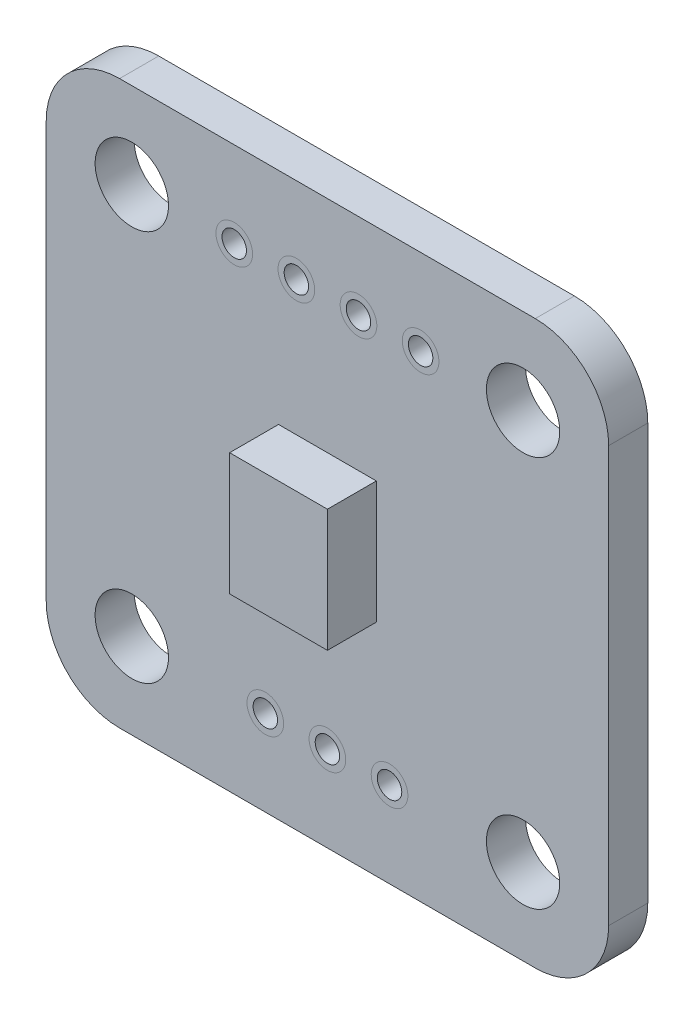
SolidWorks part; units mm, degrees
material "E-Glass Fiber"
ref_plane "Front Plane" through (0, 0, 0) normal (0, 0, 1) x (1, 0, 0)
ref_plane "Top Plane" through (0, 0, 0) normal (0, 1, 0) x (1, 0, 0)
ref_plane "Right Plane" through (0, 0, 0) normal (1, 0, 0) x (0, 0, -1)
sketch "Sketch1" plane through (0, 0, 0) normal (0, 0, 1) x (1, 0, 0)
  line L0 (0, 0) -> (0, -8) construction
  line L1 (-8.5, -11.5) -> (8.5, -11.5)
  line L2 (-11.5, -8.5) -> (-11.5, 8.5)
  line L3 (-8.5, 11.5) -> (8.5, 11.5)
  line L4 (11.5, -8.5) -> (11.5, 8.5)
  line L5 (-11.5, -11.5) -> (11.5, 11.5) construction
  line L6 (-11.5, 11.5) -> (11.5, -11.5) construction
  line L7 (-8, -8) -> (8, -8) construction
  line L8 (-8, -8) -> (-8, 8) construction
  line L9 (-8, 8) -> (8, 8) construction
  line L10 (8, -8) -> (8, 8) construction
  line L11 (-8, -8) -> (8, 8) construction
  line L12 (-8, 8) -> (8, -8) construction
  line L13 (2.54, -8) -> (-2.54, -8) construction
  line L14 (-1.27, 8) -> (1.27, 8) construction
  line L15 (-3.81, 8) -> (3.81, 8) construction
  circle A0 centre (-8, 8) radius 1.5
  circle A1 centre (8, 8) radius 1.5
  circle A2 centre (8, -8) radius 1.5
  circle A3 centre (-8, -8) radius 1.5
  arc A4 (-8.5, -11.5) -> (-11.5, -8.5) centre (-8.5, -8.5) cw
  arc A5 (8.5, -11.5) -> (11.5, -8.5) centre (8.5, -8.5) ccw
  arc A6 (8.5, 11.5) -> (11.5, 8.5) centre (8.5, 8.5) cw
  arc A7 (-11.5, 8.5) -> (-8.5, 11.5) centre (-8.5, 8.5) cw
  circle A8 centre (0, -8) radius 0.5
  circle A9 centre (-2.54, -8) radius 0.5
  circle A10 centre (2.54, -8) radius 0.5
  circle A11 centre (-1.27, 8) radius 0.5
  circle A12 centre (1.27, 8) radius 0.5
  circle A13 centre (-3.81, 8) radius 0.5
  circle A14 centre (3.81, 8) radius 0.5
  point P0 (0, 0)
  point P6 (0, 0)
  point P33 (0, -8)
  point P38 (0, 8)
  point P43 (0, 8)
  dimension "D3" = 3
  dimension "D4" = 3
  dimension "D5" = 1
  dimension "D6" = 5.08
  dimension "D7" = 2.54
  dimension "D8" = 2.54
  dimension "D1" = 23
  dimension "D2" = 16
extrude "Boss-Extrude1" add sketch "Sketch1" along normal mid plane 1.6
sketch "Sketch2" plane through (0, 0, 0.8) normal (0, 0, 1) x (1, 0, 0)
  line L1 (-2, 2.5) -> (2, 2.5)
  line L2 (-2, 2.5) -> (-2, -2.5)
  line L3 (-2, -2.5) -> (2, -2.5)
  line L4 (2, 2.5) -> (2, -2.5)
  line L5 (-2, 2.5) -> (2, -2.5) construction
  line L6 (-2, -2.5) -> (2, 2.5) construction
  point P0 (0, 0)
  dimension "D1" = 5
  dimension "D2" = 4
extrude "Boss-Extrude2" add sketch "Sketch2" along normal blind 2
sketch "Sketch3" plane through (0, 0, 0.8) normal (0, 0, 1) x (1, 0, 0)
  circle A0 centre (-3.81, 8) radius 0.75
  circle A1 centre (-1.27, 8) radius 0.75
  circle A2 centre (1.27, 8) radius 0.75
  circle A3 centre (3.81, 8) radius 0.75
  circle A4 centre (-2.54, -8) radius 0.75
  circle A5 centre (0, -8) radius 0.75
  circle A6 centre (2.54, -8) radius 0.75
  dimension "D1" = 1.5
split line "Split Line1"
